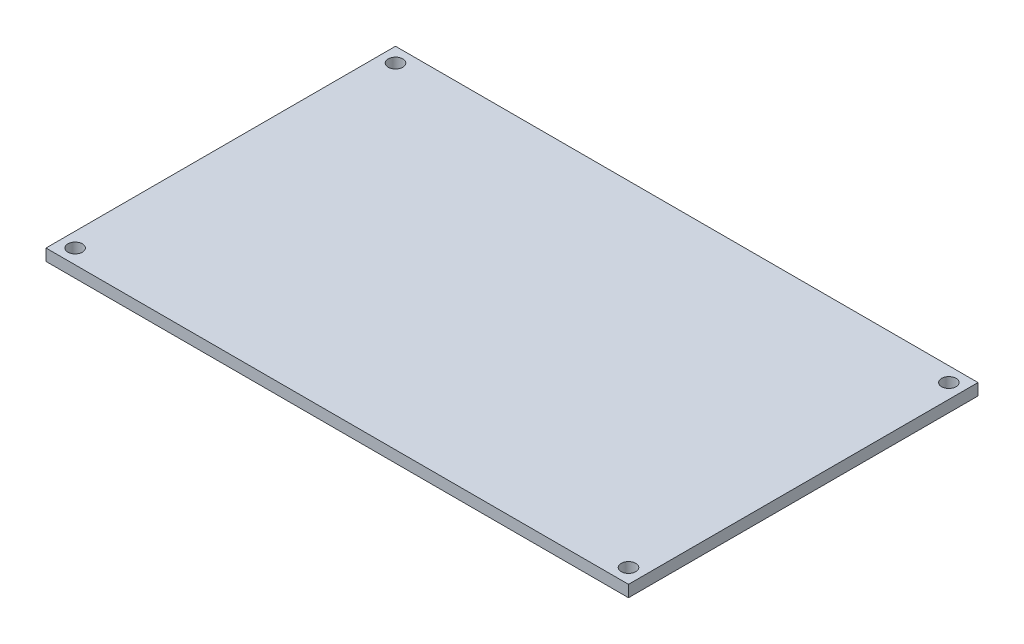
SolidWorks part; units mm, degrees
ref_plane "Front Plane" through (0, 0, 0) normal (0, 0, 1) x (1, 0, 0)
ref_plane "Top Plane" through (0, 0, 0) normal (0, 1, 0) x (1, 0, 0)
ref_plane "Right Plane" through (0, 0, 0) normal (1, 0, 0) x (0, 0, -1)
sketch "Sketch2" plane through (0, 0, 0) normal (0, 1, 0) x (1, 0, 0)
  line L2 (100, 60) -> (-100, 60)
  line L3 (100, 60) -> (100, -60)
  line L4 (100, -60) -> (-100, -60)
  line L5 (-100, 60) -> (-100, -60)
  line L6 (100, 60) -> (-100, -60) construction
  line L7 (100, -60) -> (-100, 60) construction
  point P1 (0, 0)
  dimension "D1" = 120
  dimension "D2" = 200
extrude "Boss-Extrude1" add sketch "Sketch2" along normal blind 4
sketch "Sketch3" plane through (0, 4, 0) normal (0, 1, 0) x (1, 0, 0)
  line L0 (100, 60) -> (-100, 60) construction
  line L1 (-100, -60) -> (100, -60) construction
  line L2 (-100, 60) -> (-100, -60) construction
  line L3 (100, -60) -> (100, 60) construction
  point P0 (-95, 55)
  point P1 (-95, -55)
  point P2 (95, -55)
  point P3 (95, 55)
  point P4 (-95, 55)
  dimension "D1" = 5
  dimension "D2" = 5
  dimension "D3" = 5
  dimension "D4" = 5
  dimension "D5" = 5
  dimension "D6" = 5
  dimension "D7" = 5
  dimension "D8" = 5
  dimension "D9" = 5
hole_wizard "Ø3.0mm Dowel Hole1" positions "3DSketch1" profile "Sketch4" hole size "Ø3.0" standard "ANSI Metric"
sketch3d "3DSketch1"
  point P0 (-95, 4, -55)
  point P3 (-95, 4, 55)
  point P6 (95, 4, 55)
  point P9 (95, 4, -55)
sketch "Sketch4" plane through (-95, 4, -55) normal (1, 0, 0) x (0, 0, 1)
  line L0 (0, 0) -> (0, 21.5022)
  line L1 (0, 21.5022) -> (2.5, 20)
  line L2 (2.5, 20) -> (2.5, 0)
  line L5 (2.5, 0) -> (0, 0)
  line L10 (0, 21.5022) -> (-2.5, 20) construction
  line L11 (0, -6.35) -> (0, 107.95) construction
  dimension "Hole Dia." = 5
  dimension "Hole Depth" = 20
  dimension "Drill Angle" = 118
